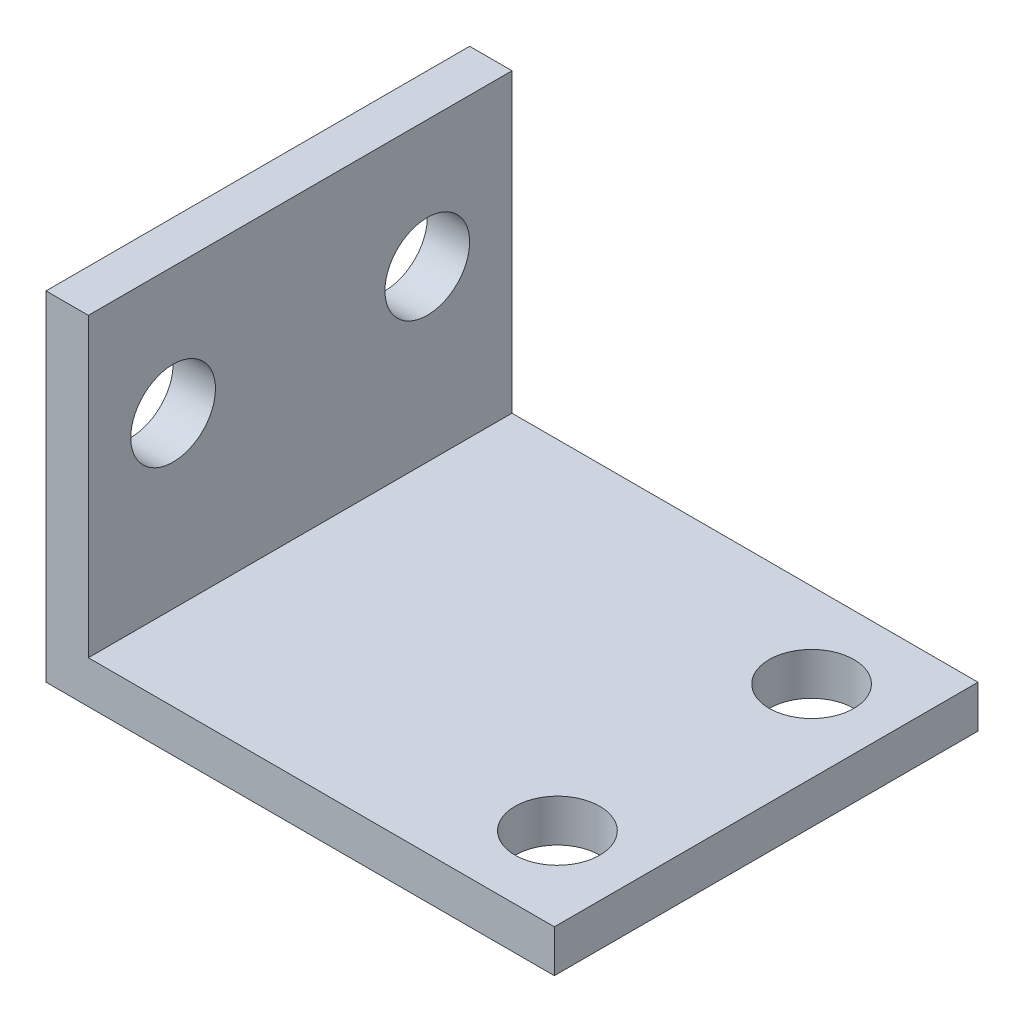
SolidWorks part; units mm, degrees
ref_plane "Front Plane" through (0, 0, 0) normal (0, 0, 1) x (1, 0, 0)
ref_plane "Top Plane" through (0, 0, 0) normal (0, 1, 0) x (1, 0, 0)
ref_plane "Right Plane" through (0, 0, 0) normal (1, 0, 0) x (0, 0, -1)
sketch "Sketch1" plane through (0, 0, 0) normal (0, 0, 1) x (1, 0, 0)
  line L0 (0, 0) -> (0, 25.4)
  line L1 (0, 25.4) -> (3.175, 25.4)
  line L2 (3.175, 25.4) -> (3.175, 3.175)
  line L3 (3.175, 3.175) -> (38.1, 3.175)
  line L4 (38.1, 3.175) -> (38.1, 0)
  line L5 (38.1, 0) -> (0, 0)
  dimension "D1" = 3.175
  dimension "D2" = 3.175
  dimension "D3" = 38.1
  dimension "D4" = 25.4
extrude "Boss-Extrude1" add sketch "Sketch1" along normal blind 31.75
sketch "Sketch2" plane through (0, 3.175, 0) normal (0, 1, 0) x (1, 0, 0)
  line L0 (38.1, -15.875) -> (3.175, -15.875) construction
  line L1 (38.1, -31.75) -> (38.1, 0) construction
  line L2 (3.175, -31.75) -> (3.175, 0) construction
  circle A0 centre (31.9786, -6.35) radius 3.175
  circle A1 centre (31.9786, -25.4) radius 3.175
  dimension "D1" = 6.35
  dimension "D3" = 19.05
  dimension "D2" = 19.05
  dimension "D4" = 31.9786
extrude "Cut-Extrude1" cut sketch "Sketch2" against normal through all
sketch "Sketch3" plane through (3.175, 0, 0) normal (1, 0, 0) x (0, 0, -1)
  line L0 (-15.875, 25.4) -> (-15.875, 3.175) construction
  line L1 (-31.75, 25.4) -> (0, 25.4) construction
  line L2 (-31.75, 3.175) -> (0, 3.175) construction
  line L3 (-31.75, 0) -> (0, 0) construction
  circle A0 centre (-25.4, 15.875) radius 3.175
  circle A1 centre (-6.35, 15.875) radius 3.175
  dimension "D1" = 6.35
  dimension "D2" = 19.05
  dimension "D3" = 15.875
  dimension "D4" = 19.05
extrude "Cut-Extrude2" cut sketch "Sketch3" against normal through all
